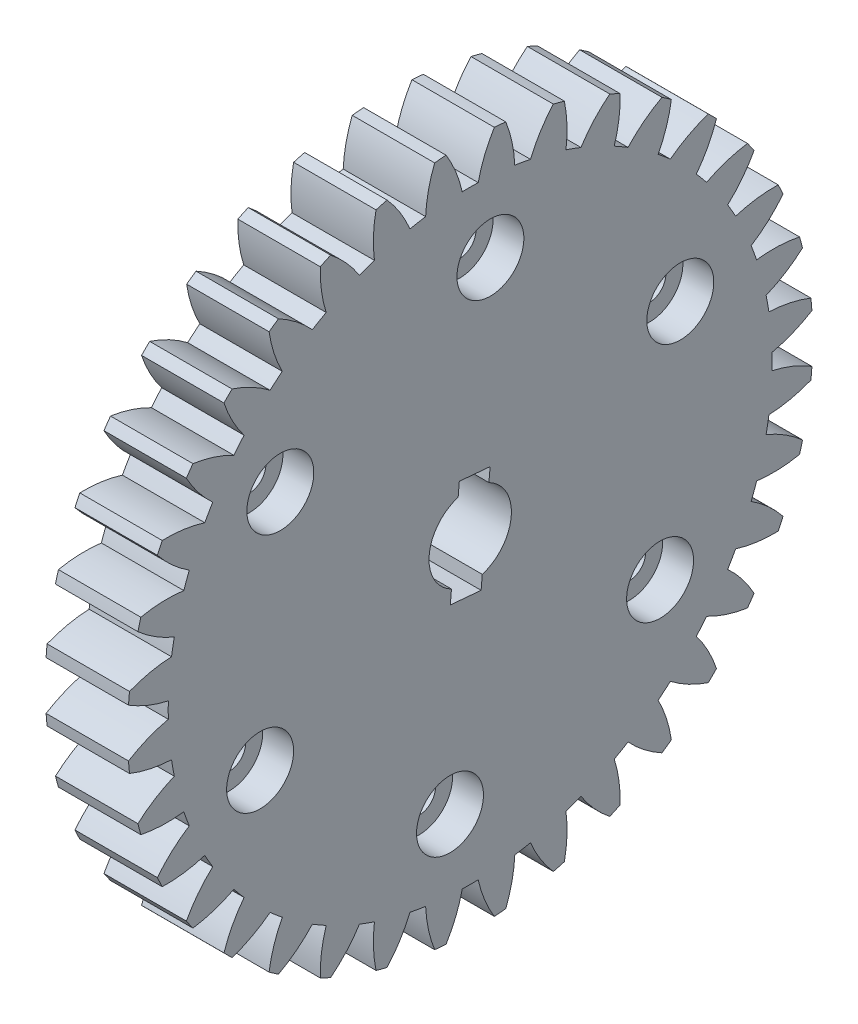
SolidWorks part; units mm, degrees
material "PLA personnalisé"
ref_plane "Plane1" through (0, 0, 0) normal (0, 0, 1) x (1, 0, 0)
ref_plane "Plane2" through (0, 0, 0) normal (0, 1, 0) x (1, 0, 0)
ref_plane "Plane3" through (0, 0, 0) normal (1, 0, 0) x (0, 0, -1)
other "Configuration Table"
sketch "HoldingSke" plane through (0, 0, 0) normal (0, 1, 0) x (1, 0, 0)
  line L0 (0, 0) -> (0.4623, -0.3359)
  line L1 (-15, 0) -> (100, 0) construction
  line L2 (0, 0) -> (-2.1039, 2.3779)
  line L3 (0, 0) -> (-11.863, 4.5341)
  line L4 (0, 0) -> (6.9867, 5.0761)
  line L5 (0, 0) -> (-46.8476, -17.4728)
  line L6 (0, 0) -> (-6.6317, -4.4744)
  line L7 (-2.1039, 2.3779) -> (8.6586, 51.2059)
  line L8 (-76.2, 54.61) -> (-74.8, 54.61)
  line L9 (-71.009, 38.7566) -> (-53.1078, 45.2721)
  line L10 (-76.2, 71.12) -> (104.1128, 71.12)
  line L11 (0, 0) -> (-8, 0)
  line L12 (-76.2, 101.6) -> (-76.147, 101.6)
  line L13 (24.9733, 27.94) -> (52.9518, 28.4284)
  line L14 (24.9733, 27.94) -> (24.9743, 27.94)
  line L15 (24.9733, 27.94) -> (100.4006, 29.5858)
  line L16 (-63.627, -1.75) -> (-12.827, -1.75)
  circle A0 centre (0, 0) radius 4
  circle A1 centre (0, 0) radius 29.3115
  circle A2 centre (0, 0) radius 37.5
  circle A3 centre (0, 0) radius 4
  dimension "MHD" = 58.623
  dimension "Hub_dia" = 75
  dimension "Bore" = 8
  dimension "MBD" = 8
  dimension "Num_teeth" = 36
  dimension "Pitch" = 0.5714
  dimension "Overall_len" = 50
  dimension "Show_teeth" = 36
  dimension "Thickness" = 8
  dimension "OAL" = 50.0001
  dimension "T_dim" = 1.4
  dimension "Ap" = 20
  dimension "H" = 19.05
  dimension "Pitch_radius" = 180.3128
  dimension "Width" = 8
  dimension "Backlash" = 0.053
  dimension "Addendum_fac" = 1
  dimension "Dedendum_fac" = 1.25
  dimension "Clearance_fac" = 0.25
  dimension "Dedendum_add" = 0.001
  dimension "Module" = 1.75
sketch "BasProSke" plane through (0, 0, 0) normal (0, 1, 0) x (1, 0, 0)
  line L0 (-10, 0) -> (60, 0) construction
  line L1 (0, 0) -> (0, 33.25)
  line L2 (0, 0) -> (8, 0)
  line L3 (8, 0) -> (8, 33.25)
  line L4 (8, 33.25) -> (0, 33.25)
  dimension "Thickness" = 8
  dimension "Diameter" = 66.5
revolve "Base-Revolve" add sketch "BasProSke" angle 360 about L0
sketch "TooCutSke" plane through (0, 0, 0) normal (1, 0, 0) x (0, 0, -1)
  line L1 (0, 0) -> (0, 107) construction
  line L2 (0, 0) -> (-1.4667, 31.4658) construction
  line L3 (0, 0) -> (-5.4863, 62.7083) construction
  line L4 (-1.4667, 31.4658) -> (-2.7431, 31.3542) construction
  arc A0 (0.7738, 29.3013) -> (-0.7738, 29.3013) centre (0, 0) ccw
  arc A1 (2.3593, 33.1917) -> (-2.3593, 33.1917) centre (0, 0) ccw
  circle A2 centre (0, 0) radius 31.5 construction
  circle A3 centre (0, 0) radius 29.6003 construction
  arc A4 (-0.7738, 29.3013) -> (-2.3593, 33.1917) centre (-13.0715, 26.5578) ccw
  arc A5 (2.3593, 33.1917) -> (0.7738, 29.3013) centre (13.0715, 26.5578) ccw
  dimension "Root_dia" = 58.623
  dimension "Overcut_dia" = 66.5508
  dimension "Pitch_dia" = 63
  dimension "Base_dia" = 59.2006
  dimension "Flank_rad" = 12.6
  dimension "Half_ang" = 5
  dimension "Half_CT" = 1.2813
extrude "ToothCut" cut sketch "TooCutSke" along normal through all
fillet "Breaks" [suppressed] radius 0.035
fillet "RootFillets" [suppressed] radius 0.4385
pattern_circular "TeethCuts" count 36 every 10 about axis through (-10, 0, 0) along (1, 0, 0) of "ToothCut", "RootFillets", "Breaks"
sketch "HubNeaOneSke" plane through (0, 0, 0) normal (-1, 0, 0) x (0, 0, 1)
  circle A0 centre (0, 0) radius 29.3115
  dimension "Diameter" = 58.623
extrude "HubNearOne" [suppressed] add sketch "HubNeaOneSke" along normal blind 42.0001
sketch "HubNeaBotSke" plane through (0, 0, 0) normal (-1, 0, 0) x (0, 0, 1)
  circle A0 centre (0, 0) radius 29.3115
  dimension "Diameter" = 58.623
extrude "HubNearBoth" [suppressed] add sketch "HubNeaBotSke" along normal blind 21
ref_plane "FarPln" through (8, 0, 0) normal (1, 0, 0) x (0, 0, -1)
sketch "HubFarSke" plane through (8, 0, 0) normal (1, 0, 0) x (0, 0, -1)
  circle A0 centre (0, 0) radius 29.3115
  dimension "Diameter" = 58.623
extrude "HubFar" [suppressed] add sketch "HubFarSke" along normal blind 21
sketch "BorSke" plane through (0, 0, 0) normal (1, 0, 0) x (0, 0, -1)
  circle A0 centre (0, 0) radius 4
  dimension "Diameter" = 8
extrude "Bore" cut sketch "BorSke" along normal mid plane 100.0001
sketch "KeySke" plane through (0, 0, 0) normal (1, 0, 0) x (0, 0, -1)
  line L0 (-1.5, 0) -> (-1.5, 5.4)
  line L1 (-1.5, 5.4) -> (1.5, 5.4)
  line L2 (1.5, 5.4) -> (1.5, 0)
  line L3 (0, 0) -> (0, 34) construction
  line L4 (-1.5, 0) -> (1.5, 0)
  dimension "Offset" = 5.4
  dimension "Width" = 3
extrude "Keyway" [suppressed] cut sketch "KeySke" along normal mid plane 100.0001
pattern_circular "Keyway2" [suppressed] count 2 every 90 about axis through (-10, 0, 0) along (1, 0, 0)
sketch "Esquisse2" plane through (8, 0, 0) normal (1, 0, 0) x (0, 0, -1)
  line L0 (2.8979, 33.1235) -> (0, 0) construction
  line L1 (1.3673, 15.6288) -> (2.5547, 29.2)
  arc A0 (3.4508, 33.0704) -> (2.3442, 33.1673) centre (0, 0) ccw construction
  circle A1 centre (0, 0) radius 29.3115
  circle A2 centre (0, 0) radius 15.6885
  circle A3 centre (1.961, 22.4144) radius 1.6
  circle A4 centre (0, 0) radius 22.5
  dimension "D1" = 3.2
  dimension "D2" = 45
extrude "Enlèv. mat.-Extru.2" cut sketch "Esquisse2" against normal blind 10 contours A3
sketch "Esquisse3" plane through (8, 0, 0) normal (1, 0, 0) x (0, 0, -1)
  circle A0 centre (1.961, 22.4144) radius 3.25
  dimension "D1" = 6.5
extrude "Enlèv. mat.-Extru.3" cut sketch "Esquisse3" against normal blind 3
pattern_circular "Répétition circulaire1" count 6 over 360 about axis through (0, 0, 0) along (1, 0, 0) of "Enlèv. mat.-Extru.2", "Enlèv. mat.-Extru.3"
sketch "Esquisse4" plane through (8, 0, 0) normal (1, 0, 0) x (0, 0, -1)
  line L0 (0, 0) -> (1.961, 22.4144) construction
  line L1 (1.0585, -5.1117) -> (-1.9301, -4.8502)
  line L2 (1.0585, -5.1117) -> (1.9301, 4.8502)
  line L3 (1.9301, 4.8502) -> (-1.0585, 5.1117)
  line L4 (-1.9301, -4.8502) -> (-1.0585, 5.1117)
  line L5 (1.0585, -5.1117) -> (-1.0585, 5.1117) construction
  line L6 (1.9301, 4.8502) -> (-1.9301, -4.8502) construction
  point P0 (0, 0)
  dimension "D1" = 10
  dimension "D2" = 3
extrude "Enlèv. mat.-Extru.4" cut sketch "Esquisse4" against normal blind 10
equation "' \"Module@HoldingSke\" = 6.35"
equation "' \"Num_teeth@HoldingSke\" = 12"
equation "' \"Ap@HoldingSke\" =  20"
equation "' \"Ap@HoldingSke\" = 20"
equation "' \"Width@HoldingSke\" = 0.5 * 25.4"
equation "' \"Hub_dia@HoldingSke\"= 1 * 25.4"
equation "' \"Hub_dia@HoldingSke\" = 1 * 25.4"
equation "' \"Overall_len@HoldingSke\" = 1.0 * 25.4"
equation "' \"Bore@HoldingSke\" = 0.75 * 25.4"
equation "' \"T_dim@HoldingSke\" = 0.1 * 25.4"
equation "' \"Width@KeySke\" = 0.25 * 25.4"
equation "' \"Show_teeth@HoldingSke\" = 13"
equation "' \"Backlash@HoldingSke\" = 0.009 * 25.4"
equation "' \"Addendum_fac@HoldingSke\" = 1.0"
equation "' \"Dedendum_fac@HoldingSke\" = 1.25"
equation "' \"Dedendum_add@HoldingSke\" = 0.00005 * 25.4"
equation "' \"Clearance_fac@HoldingSke\" = 0.25"
equation "\"Pitch@HoldingSke\" = 1 / \"Module@HoldingSke\""
equation "\"Overcut_dia@TooCutSke\" = (\"Num_teeth@HoldingSke\" + 2 * \"Addendum_fac@HoldingSke\") / \"Pitch@HoldingSke\" + 0.002 * 25.4"
equation "\"Pitch_dia@TooCutSke\" = \"Num_teeth@HoldingSke\" / \"Pitch@HoldingSke\""
equation "\"Base_dia@TooCutSke\" = \"Num_teeth@HoldingSke\" / \"Pitch@HoldingSke\" * cos((\"Ap@HoldingSke\"  * 3.14159265 / 180))"
equation "\"Root_dia@TooCutSke\" = (\"Num_teeth@HoldingSke\" + 2) / \"Pitch@HoldingSke\" - 2 * (\"Addendum_fac@HoldingSke\" + \"Dedendum_fac@HoldingSke\") / \"Pitch@HoldingSke\" - \"Dedendum_add@HoldingSke\" * 2"
equation "\"Half_ang@TooCutSke\" = 180 / \"Num_teeth@HoldingSke\""
equation "\"Half_CT@TooCutSke\" = \"Num_teeth@HoldingSke\" / \"Pitch@HoldingSke\" * sin((3.14159265 / 2 / \"Num_teeth@HoldingSke\")) / 2 - 7 * \"Backlash@HoldingSke\" / 4"
equation "\"Flank_rad@TooCutSke\" = \"Num_teeth@HoldingSke\" / \"Pitch@HoldingSke\" / 5"
equation "\"Radius@RootFillets\" = \"Clearance_fac@HoldingSke\" / \"Pitch@HoldingSke\" + \"Dedendum_add@HoldingSke\""
equation "\"Break_rad@Breaks\" = 0.02 / \"Pitch@HoldingSke\""
equation "\"Thickness@HoldingSke\" = \"Width@HoldingSke\""
equation "\"OAL@HoldingSke\" = \"Thickness@HoldingSke\""
equation "\"MHD@HoldingSke\" = (\"Num_teeth@HoldingSke\" + 2) / \"Pitch@HoldingSke\" - 2 * (\"Addendum_fac@HoldingSke\" + \"Dedendum_fac@HoldingSke\")  / \"Pitch@HoldingSke\" - \"Dedendum_add@HoldingSke\" * 2"
equation "\"MBD@HoldingSke\" = (\"Num_teeth@HoldingSke\" + 2) / \"Pitch@HoldingSke\" - 2 * (\"Addendum_fac@HoldingSke\" + \"Dedendum_fac@HoldingSke\")  / \"Pitch@HoldingSke\" - \"Dedendum_add@HoldingSke\" * 2 - 0.002 * 25.4"
equation "\"MHD@HoldingSke\" = ((sgn( \"MHD@HoldingSke\" - \"Hub_dia@HoldingSke\" )-1)*( \"MHD@HoldingSke\" - \"Hub_dia@HoldingSke\" ))/-2+ \"Hub_dia@HoldingSke\""
equation "\"MBD@HoldingSke\" = ((sgn( \"MBD@HoldingSke\" - \"Bore@HoldingSke\" )-1)*( \"MBD@HoldingSke\" - \"Bore@HoldingSke\" ))/-2+ \"Bore@HoldingSke\""
equation "\"OAL@HoldingSke\" = ((sgn( \"OAL@HoldingSke\" - \"Overall_len@HoldingSke\" )+1)*( \"OAL@HoldingSke\" - \"Overall_len@HoldingSke\" ))/2 + \"Overall_len@HoldingSke\" + 0.000002 * 25.4"
equation "\"Num_teeth@TeethCuts\" = int( \"Show_teeth@HoldingSke\" ) + 1"
equation "\"Num_teeth@TeethCuts\" = ((sgn( \"Num_teeth@TeethCuts\" - \"Num_teeth@HoldingSke\" )-1)*( \"Num_teeth@TeethCuts\" - \"Num_teeth@HoldingSke\" ))/-2+ \"Num_teeth@HoldingSke\""
equation "\"Num_teeth@TeethCuts\" = ((sgn( \"Num_teeth@TeethCuts\" - 2.0)+1)*( \"Num_teeth@TeethCuts\" - 2.0))/2 +2.0"
equation "\"Angle@TeethCuts\" = 360.0 / \"Num_teeth@HoldingSke\""
equation "\"Diameter@BasProSke\" = (\"Num_teeth@HoldingSke\" + 2 * \"Addendum_fac@HoldingSke\") / \"Pitch@HoldingSke\""
equation "\"Thickness@BasProSke\"  = \"Thickness@HoldingSke\""
equation "' \"Fillet_rad@BasProSke\" =  \"Thickness@HoldingSke\" * 0.05"
equation "' \"Fillet_rad@BasProSke\" = \"Thickness@HoldingSke\" * 0.05"
equation "\"MHD@HoldingSke\" = ((sgn( \"MHD@HoldingSke\" - \"Root_dia@TooCutSke\" )-1)*( \"MHD@HoldingSke\" - \"Root_dia@TooCutSke\" ))/-2+ \"Root_dia@TooCutSke\""
equation "\"Diameter@HubNeaOneSke\" = \"MHD@HoldingSke\""
equation "\"Length@HubNearOne\" = \"OAL@HoldingSke\" - \"Thickness@BasProSke\""
equation "\"Diameter@HubNeaBotSke\" = \"MHD@HoldingSke\""
equation "\"Length@HubNearBoth\" = ( \"OAL@HoldingSke\" - \"Thickness@BasProSke\" ) / 2.0"
equation "\"Thickness@FarPln\" = \"Thickness@BasProSke\""
equation "\"Diameter@HubFarSke\" = \"MHD@HoldingSke\""
equation "\"Length@HubFar\" = ( \"OAL@HoldingSke\" - \"Thickness@BasProSke\" ) / 2.0"
equation "\"Diameter@BorSke\" = \"MBD@HoldingSke\""
equation "\"D1@Bore\" = \"OAL@HoldingSke\" * 2.0"
equation "\"D1@Keyway\" = \"OAL@HoldingSke\" * 2.0"
equation "\"Offset@KeySke\" = \"T_dim@HoldingSke\" + \"MBD@HoldingSke\" / 2.0"
